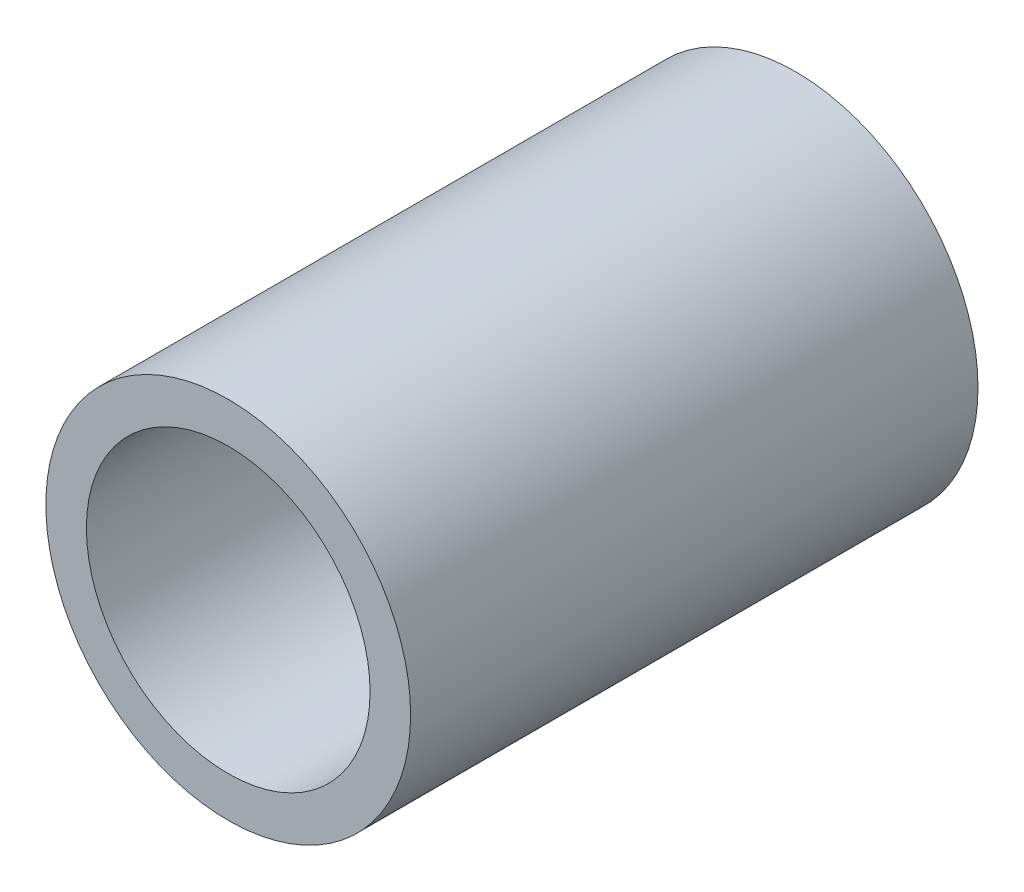
SolidWorks part; units mm, degrees
ref_plane "前视基准面" through (0, 0, 0) normal (0, 0, 1) x (1, 0, 0)
ref_plane "上视基准面" through (0, 0, 0) normal (0, 1, 0) x (1, 0, 0)
ref_plane "右视基准面" through (0, 0, 0) normal (1, 0, 0) x (0, 0, -1)
sketch "草图1" plane through (0, 0, 0) normal (0, 0, 1) x (1, 0, 0)
  circle A0 centre (0, 0) radius 2.25
  circle A1 centre (0, 0) radius 1.75
  dimension "D1" = 3.5
  dimension "D2" = 4.5
extrude "凸台-拉伸1" add sketch "草图1" along normal blind 7
